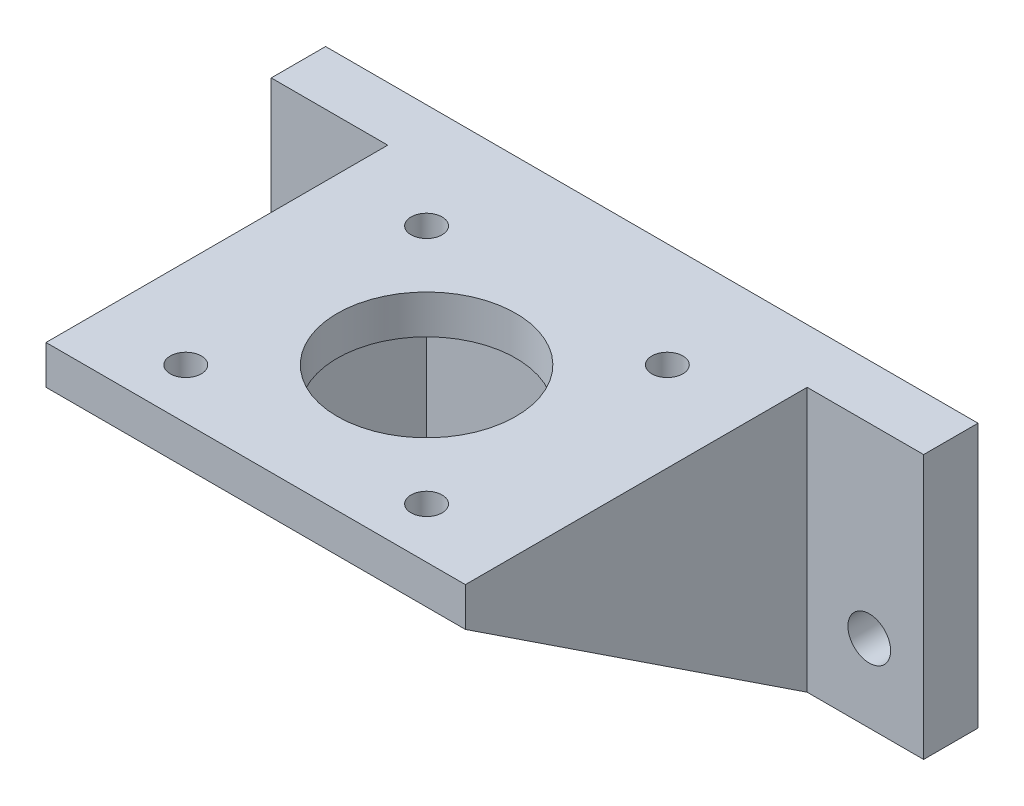
SolidWorks part; units mm, degrees
ref_plane "Front Plane" through (0, 0, 0) normal (0, 0, 1) x (1, 0, 0)
ref_plane "Top Plane" through (0, 0, 0) normal (0, 1, 0) x (1, 0, 0)
ref_plane "Right Plane" through (0, 0, 0) normal (1, 0, 0) x (0, 0, -1)
sketch "Sketch2" plane through (0, 0, 0) normal (0, 1, 0) x (1, 0, 0)
  line L1 (0, 0) -> (44, 0)
  line L2 (0, 0) -> (0, 44)
  line L3 (0, 44) -> (44, 44)
  line L4 (44, 0) -> (44, 44)
  circle A0 centre (6.5, 37.5) radius 2
  circle A1 centre (6.5, 6.5) radius 2
  circle A2 centre (37.5, 6.5) radius 2
  circle A3 centre (37.5, 37.5) radius 2
  circle A4 centre (22, 22) radius 11.5
  dimension "D2" = 4
  dimension "D10" = 23
  dimension "D12" = 22
  dimension "D1" = 44
  dimension "D3" = 31
  dimension "D4" = 31
  dimension "D5" = 31
  dimension "D6" = 31
  dimension "D7" = 31
  dimension "D8" = 6.5
  dimension "D9" = 6.5
  dimension "D11" = 22
extrude "Boss-Extrude1" add sketch "Sketch2" along normal blind 5
sketch "Sketch4" plane through (0, 0, -44) normal (0, 0, -1) x (-1, 0, 0)
  line L1 (-64, 5) -> (20, 5)
  line L2 (-64, 5) -> (-64, -29)
  line L3 (-64, -29) -> (20, -29)
  line L4 (20, 5) -> (20, -29)
  line L5 (0, 5) -> (0, 0) construction
  circle A0 centre (-57, -19) radius 2.75
  circle A1 centre (13, -19) radius 2.75
  dimension "D3" = 5.5
  dimension "D4" = 5.5
  dimension "D1" = 34
  dimension "D2" = 84
  dimension "D5" = 10
  dimension "D6" = 10
  dimension "D7" = 70
  dimension "D8" = 7
  dimension "D9" = 20
extrude "Boss-Extrude2" add sketch "Sketch4" along normal blind 7
sketch "Sketch5" plane through (44, 0, 0) normal (1, 0, 0) x (0, 0, -1)
  line L0 (0, 5) -> (51, 5)
  line L1 (51, 5) -> (51, -29)
  line L2 (51, -29) -> (44, -29)
  line L3 (44, -29) -> (0, 0)
  line L4 (0, 0) -> (0, 5)
  point P4 (0, 0)
  point P11 (0, 0)
  point P12 (0, 0)
extrude "Boss-Extrude3" add sketch "Sketch5" along normal blind 5
sketch "Sketch6" plane through (0, 0, 0) normal (-1, 0, 0) x (0, 0, 1)
  line L0 (-51, 5) -> (0, 5)
  line L1 (0, 5) -> (0, 0)
  line L2 (0, 0) -> (-44, -29)
  line L3 (-44, -29) -> (-51, -29)
  line L4 (-51, -29) -> (-51, 5)
  point P4 (0, 0)
  point P11 (0, 0)
  point P12 (0, 0)
extrude "Boss-Extrude4" add sketch "Sketch6" along normal blind 5
